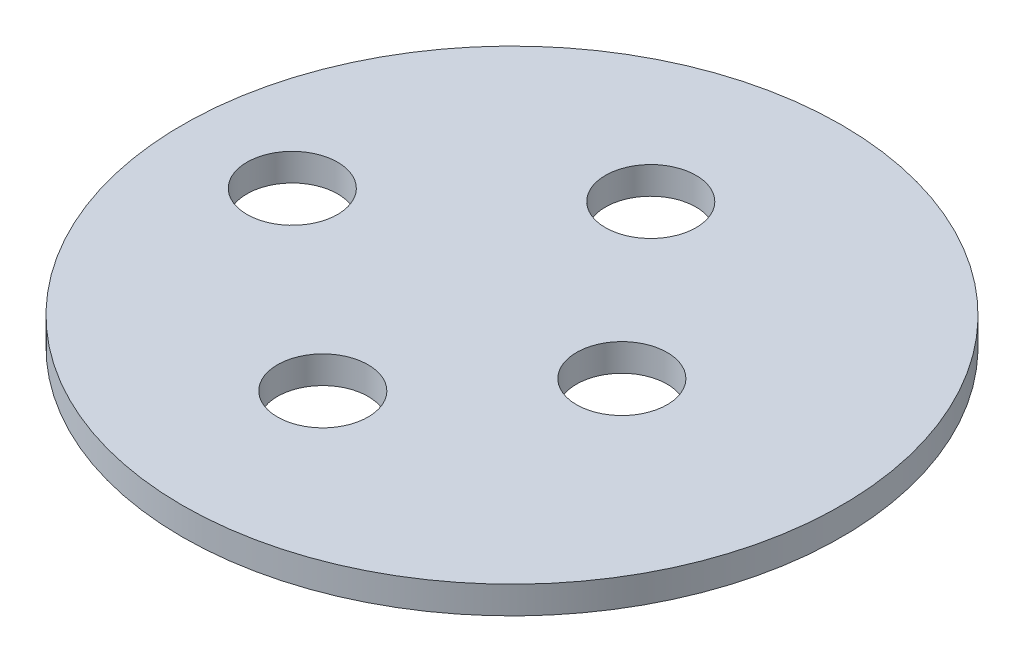
SolidWorks part; units mm, degrees
ref_plane "Front Plane" through (0, 0, 0) normal (0, 0, 1) x (1, 0, 0)
ref_plane "Top Plane" through (0, 0, 0) normal (0, 1, 0) x (1, 0, 0)
ref_plane "Right Plane" through (0, 0, 0) normal (1, 0, 0) x (0, 0, -1)
sketch "Sketch1" plane through (0, 0, 0) normal (0, 1, 0) x (1, 0, 0)
  line L0 (-3.0812, -0.6374) -> (-3.0812, 5.0364) construction
  line L1 (-3.0812, 5.0364) -> (-3.0812, -7.1626) construction
  line L2 (-3.0812, -0.6374) -> (17.9338, -0.6374) construction
  line L3 (-3.0812, -0.6374) -> (-17.4056, -0.6374) construction
  line L4 (-1.0812, -0.6374) -> (-1.0812, 11.5001) construction
  line L5 (-1.0812, 11.5001) -> (-1.0812, -13.9161) construction
  line L6 (0.9188, -0.6374) -> (0.9188, 11.8553) construction
  line L7 (0.9188, 11.8553) -> (0.9188, -14.2318) construction
  line L8 (-0.1383, 11.5001) -> (-0.1383, -13.0503) construction
  circle A2 centre (-0.1383, 5.4721) radius 1.65
  circle A4 centre (-0.1383, -6.4699) radius 1.65
  circle A9 centre (0.9188, -0.6374) radius 12
  circle A10 centre (-7.0812, -0.6374) radius 1.65
  circle A11 centre (4.9188, -0.6374) radius 1.65
  point P1 (0, 0)
  point P13 (0, 0)
  dimension "D5" = 3.3
  dimension "D7" = 3.3
  dimension "D12" = 24
  dimension "D13" = 3.3
  dimension "D14" = 3.3
  dimension "D3" = 2
  dimension "D15" = 6
  dimension "D16" = 6
extrude "Boss-Extrude1" add sketch "Sketch1" against normal blind 1 contours A10 | A4 | A2 | A11 | A9
equation "\"R\"= 63mm"
equation "\"E\"= 2mm"
equation "\"Rr\"= 5"
equation "\"N\"= 22"
equation "\"M5\"= 5"
equation "\"SMALL_BEARING_DEPTH\"= 6MM"
